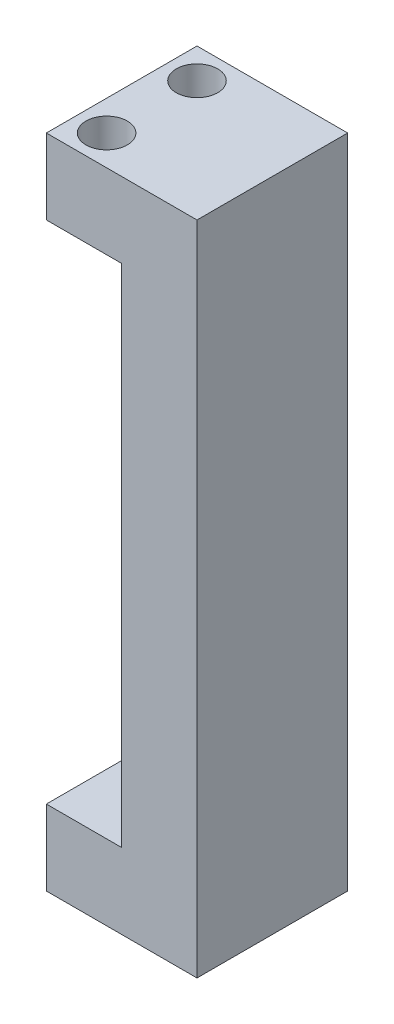
SolidWorks part; units mm, degrees
ref_plane "前视基准面" through (0, 0, 0) normal (0, 0, 1) x (1, 0, 0)
ref_plane "上视基准面" through (0, 0, 0) normal (0, 1, 0) x (1, 0, 0)
ref_plane "右视基准面" through (0, 0, 0) normal (1, 0, 0) x (0, 0, -1)
sketch "草图1" plane through (0, 0, 0) normal (0, 0, 1) x (1, 0, 0)
  line L0 (-20, 30.15) -> (-15, 30.15)
  line L1 (-15, 30.15) -> (-15, 77.15)
  line L2 (-15, 77.15) -> (-20, 77.15)
  line L3 (0, 87.15) -> (-20, 87.15)
  line L4 (0, 0) -> (0, 87.15)
  line L5 (-20, 0) -> (0, 0)
  line L6 (-20, 30.15) -> (-20, 0)
  line L7 (-20, 87.15) -> (-20, 77.15)
extrude "凸台-拉伸1" add sketch "草图1" along normal blind 20
hole_wizard "M4 螺纹孔1" positions "草图2" profile "草图3" tap size "M4" standard "ISO"
sketch "草图2" plane through (0, 87.15, 0) normal (0, 1, 0) x (1, 0, 0)
  line L0 (-10, 0) -> (-10, -20) construction
  line L1 (0, 0) -> (-20, 0) construction
  line L2 (0, -20) -> (-20, -20) construction
  line L3 (-10, -20) -> (-10, -10) construction
  line L4 (-10, -10) -> (0, -10) construction
  line L5 (0, -20) -> (0, 0) construction
  point P0 (-15, -5)
  point P2 (-5, -5)
  point P4 (-15, -15)
  point P6 (-5, -15)
  dimension "D1" = 10
  dimension "D2" = 10
sketch "草图3" plane through (-15, 87.15, 5) normal (1, 0, 0) x (0, 0, 1)
  line L0 (0, 0) -> (0, 6.9914)
  line L1 (0, 6.9914) -> (1.65, 6)
  line L2 (1.65, 6) -> (1.65, 0)
  line L5 (1.65, 0) -> (0, 0)
  line L10 (0, 6.9914) -> (-1.65, 6) construction
  line L11 (0, -6.35) -> (0, 107.95) construction
  dimension "螺纹孔钻头直径" = 3.3
  dimension "螺纹孔钻头深度" = 6
  dimension "导头角度" = 118
cosmetic thread "孔螺蚊线1" parameters "D1"=6, "D2"=4
cosmetic thread "孔螺蚊线2" parameters "D1"=6, "D2"=4
cosmetic thread "孔螺蚊线3" parameters "D1"=6, "D2"=4
cosmetic thread "孔螺蚊线4" parameters "D1"=6, "D2"=4
ref_plane "基准面2" through (0, 43.575, 0) normal (0, 1, 0) x (1, 0, 0)
mirror "镜向1" about plane through (0, 43.575, 0) normal (0, 1, 0) of "M4 螺纹孔1"
sketch "草图5" plane through (0, 87.15, 0) normal (0, 1, 0) x (1, 0, 0)
  line L1 (-20, -20) -> (0, -20)
  line L2 (-20, -20) -> (-20, 0)
  line L3 (-20, 0) -> (0, 0)
  line L4 (0, -20) -> (0, 0)
extrude "凸台-拉伸2" add sketch "草图5" against normal blind 10
sketch "草图6" plane through (-15, 0, 0) normal (-1, 0, 0) x (0, 0, 1)
  line L1 (0, 30.15) -> (20, 30.15)
  line L2 (0, 30.15) -> (0, 77.15)
  line L3 (0, 77.15) -> (20, 77.15)
  line L4 (20, 30.15) -> (20, 77.15)
extrude "切除-拉伸2" cut sketch "草图6" against normal blind 5
sketch "草图7" plane through (0, 0, 20) normal (0, 0, 1) x (1, 0, 0)
  line L0 (-20, 30.15) -> (-20, 0) construction
  line L1 (-10, 30.15) -> (-20, 30.15)
  line L2 (-10, 30.15) -> (-10, 10)
  line L3 (-10, 10) -> (-20, 10)
  line L4 (-20, 30.15) -> (-20, 10)
  line L5 (-20, 0) -> (0, 0) construction
  dimension "D1" = 10
extrude "切除-拉伸3" cut sketch "草图7" against normal through all
sketch "草图8" plane through (0, 77.15, 0) normal (0, -1, 0) x (1, 0, 0)
  line L0 (-20, 10) -> (-13.0353, 10) construction
  line L1 (-20, 20) -> (-20, 0) construction
  circle A0 centre (-16, 4) radius 2.75
  circle A1 centre (-16, 16) radius 2.75
  dimension "D1" = 5.5
  dimension "D2" = 4
  dimension "D3" = 12
extrude "切除-拉伸4" cut sketch "草图8" against normal through all
